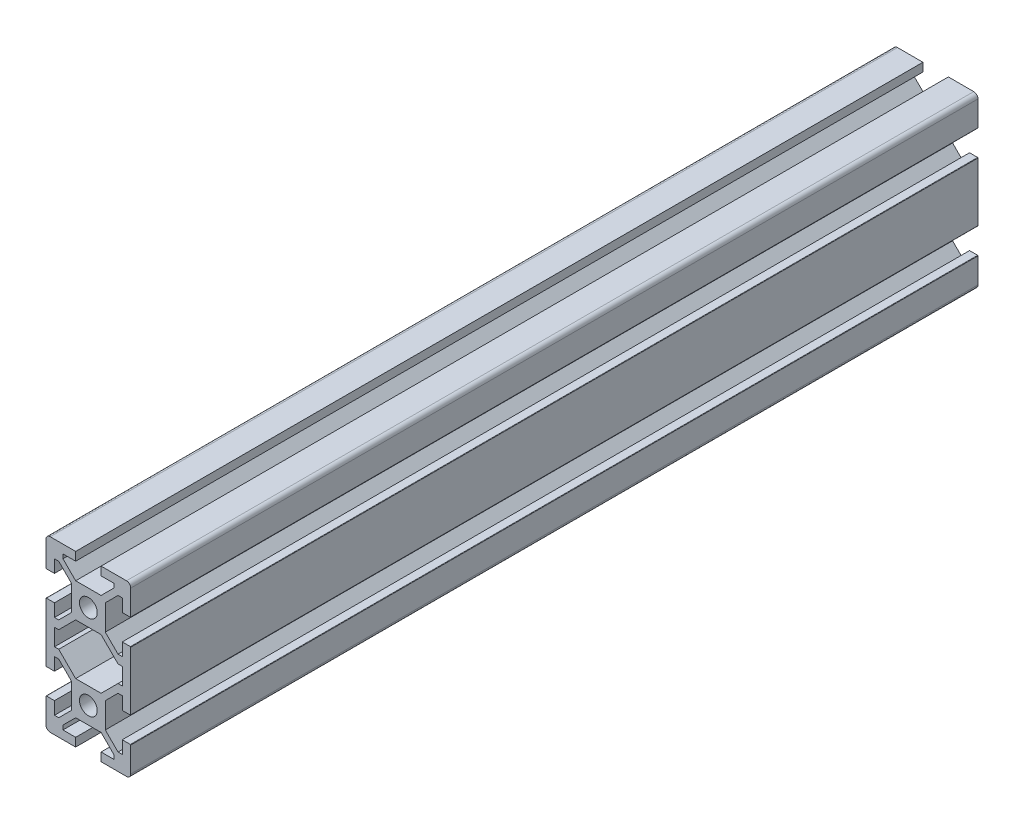
SolidWorks part; units mm, degrees
ref_plane "Front Plane" through (0, 0, 0) normal (0, 0, 1) x (1, 0, 0)
ref_plane "Top Plane" through (0, 0, 0) normal (0, 1, 0) x (1, 0, 0)
ref_plane "Right Plane" through (0, 0, 0) normal (1, 0, 0) x (0, 0, -1)
sketch "Sketch1" plane through (0, 0, 0) normal (0, 0, 1) x (1, 0, 0)
  line L0 (-7, -2) -> (-8, -2)
  line L1 (-8, -2) -> (-8, 2)
  line L2 (-8, 2) -> (-7, 2)
  line L3 (-7, 2) -> (-3, 6)
  line L4 (-3, 6) -> (3, 6)
  line L5 (3, 6) -> (7, 2)
  line L6 (7, 2) -> (8, 2)
  line L7 (8, 2) -> (8, -2)
  line L8 (8, -2) -> (7, -2)
  line L9 (7, -2) -> (3, -6)
  line L10 (3, -6) -> (-3, -6)
  line L11 (-3, -6) -> (-7, -2)
  line L12 (10, -19) -> (10, -13)
  line L13 (10, -13) -> (8, -13)
  line L14 (8, -13) -> (8, -16)
  line L15 (8, -16) -> (7, -16)
  line L16 (7, -16) -> (4, -13)
  line L17 (4, -13) -> (4, -7)
  line L18 (4, -7) -> (7, -4)
  line L19 (7, -4) -> (8, -4)
  line L20 (8, -4) -> (8, -7)
  line L21 (8, -7) -> (10, -7)
  line L22 (10, -7) -> (10, 7)
  line L23 (10, 7) -> (8, 7)
  line L24 (8, 7) -> (8, 4)
  line L25 (8, 4) -> (7, 4)
  line L26 (7, 4) -> (4, 7)
  line L27 (4, 7) -> (4, 13)
  line L28 (4, 13) -> (7, 16)
  line L29 (7, 16) -> (8, 16)
  line L30 (8, 16) -> (8, 13)
  line L31 (8, 13) -> (10, 13)
  line L32 (10, 13) -> (10, 19)
  line L33 (9, 20) -> (3, 20)
  line L34 (3, 20) -> (3, 18)
  line L35 (3, 18) -> (6, 18)
  line L36 (6, 18) -> (6, 17)
  line L37 (6, 17) -> (3, 14)
  line L38 (3, 14) -> (-3, 14)
  line L39 (-3, 14) -> (-6, 17)
  line L40 (-6, 17) -> (-6, 18)
  line L41 (-6, 18) -> (-3, 18)
  line L42 (-3, 18) -> (-3, 20)
  line L43 (-3, 20) -> (-9, 20)
  line L44 (-10, 19) -> (-10, 13)
  line L45 (-10, 13) -> (-8, 13)
  line L46 (-8, 13) -> (-8, 16)
  line L47 (-8, 16) -> (-7, 16)
  line L48 (-7, 16) -> (-4, 13)
  line L49 (-4, 13) -> (-4, 7)
  line L50 (-4, 7) -> (-7, 4)
  line L51 (-7, 4) -> (-8, 4)
  line L52 (-8, 4) -> (-8, 7)
  line L53 (-8, 7) -> (-10, 7)
  line L54 (-10, 7) -> (-10, -7)
  line L55 (-10, -7) -> (-8, -7)
  line L56 (-8, -7) -> (-8, -4)
  line L57 (-8, -4) -> (-7, -4)
  line L58 (-7, -4) -> (-4, -7)
  line L59 (-4, -7) -> (-4, -13)
  line L60 (-4, -13) -> (-7, -16)
  line L61 (-7, -16) -> (-8, -16)
  line L62 (-8, -16) -> (-8, -13)
  line L63 (-8, -13) -> (-10, -13)
  line L64 (-10, -13) -> (-10, -19)
  line L65 (-9, -20) -> (-3, -20)
  line L66 (-3, -20) -> (-3, -18)
  line L67 (-3, -18) -> (-6, -18)
  line L68 (-6, -18) -> (-6, -17)
  line L69 (-6, -17) -> (-3, -14)
  line L70 (-3, -14) -> (3, -14)
  line L71 (3, -14) -> (6, -17)
  line L72 (6, -17) -> (6, -18)
  line L73 (6, -18) -> (3, -18)
  line L74 (3, -18) -> (3, -20)
  line L75 (3, -20) -> (9, -20)
  line L76 (-8, 0) -> (0, 0) construction
  line L77 (0, 0) -> (8, 0) construction
  line L78 (0, 6) -> (0, 0) construction
  line L79 (0, 0) -> (0, -6) construction
  circle A0 centre (0, -10) radius 2.1
  circle A1 centre (0, 10) radius 2.1
  arc A2 (9, -20) -> (10, -19) centre (9, -19) ccw
  arc A3 (10, 19) -> (9, 20) centre (9, 19) ccw
  arc A4 (-9, 20) -> (-10, 19) centre (-9, 19) ccw
  arc A5 (-10, -19) -> (-9, -20) centre (-9, -19) ccw
  dimension "D1" = 40
  dimension "D2" = 20
extrude "Boss-Extrude1" add sketch "Sketch1" against normal blind 200
fillet "Fillet1" radius 0.1 8 edges at (10, -13, -100) (10, -7, -100) (10, 7, -100) (10, 13, -100) (-10, 13, -100) (-10, -13, -100) (-10, -7, -100) (-10, 7, -100)
